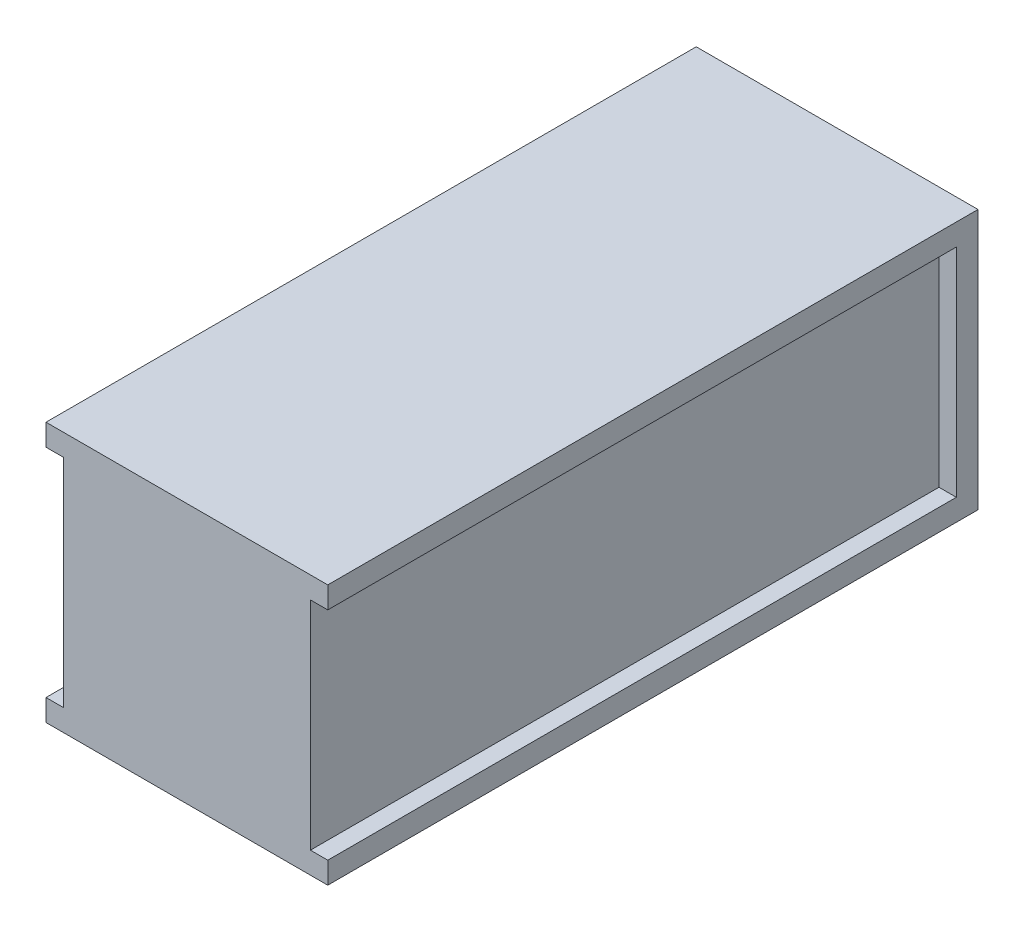
SolidWorks part; units mm, degrees
ref_plane "Plan de face" through (0, 0, 0) normal (0, 0, 1) x (1, 0, 0)
ref_plane "Plan de dessus" through (0, 0, 0) normal (0, 1, 0) x (1, 0, 0)
ref_plane "Plan de droite" through (0, 0, 0) normal (1, 0, 0) x (0, 0, -1)
sketch "Esquisse1" plane through (0, 0, 0) normal (0, 1, 0) x (1, 0, 0)
  line L0 (-32.5, 75) -> (32.5, -75) construction
  line L1 (-32.5, 75) -> (32.5, 75)
  line L2 (-32.5, 75) -> (-32.5, -75)
  line L3 (-32.5, -75) -> (32.5, -75)
  line L4 (32.5, 75) -> (32.5, -75)
  dimension "D1" = 150
  dimension "D2" = 65
extrude "Boss.-Extru.1" add sketch "Esquisse1" along normal blind 60
sketch "Esquisse2" plane through (-32.5, 0, 0) normal (-1, 0, 0) x (0, 0, 1)
  line L0 (75, 60) -> (75, 0) construction
  line L1 (75, 55) -> (-70, 55)
  line L2 (75, 55) -> (75, 5)
  line L3 (75, 5) -> (-70, 5)
  line L4 (-70, 55) -> (-70, 5)
  line L5 (75, 30) -> (-10.3389, 30) construction
  line L6 (-75, 0) -> (75, 0) construction
  line L7 (-75, 60) -> (75, 60) construction
  line L8 (-75, 60) -> (-75, 0) construction
  point P12 (0, 60)
  dimension "D1" = 5
  dimension "D2" = 5
extrude "Enlèv. mat.-Extru.1" cut sketch "Esquisse2" against normal blind 4
mirror "Symétrie1" about plane through (0, 0, 0) normal (1, 0, 0) of "Enlèv. mat.-Extru.1"
